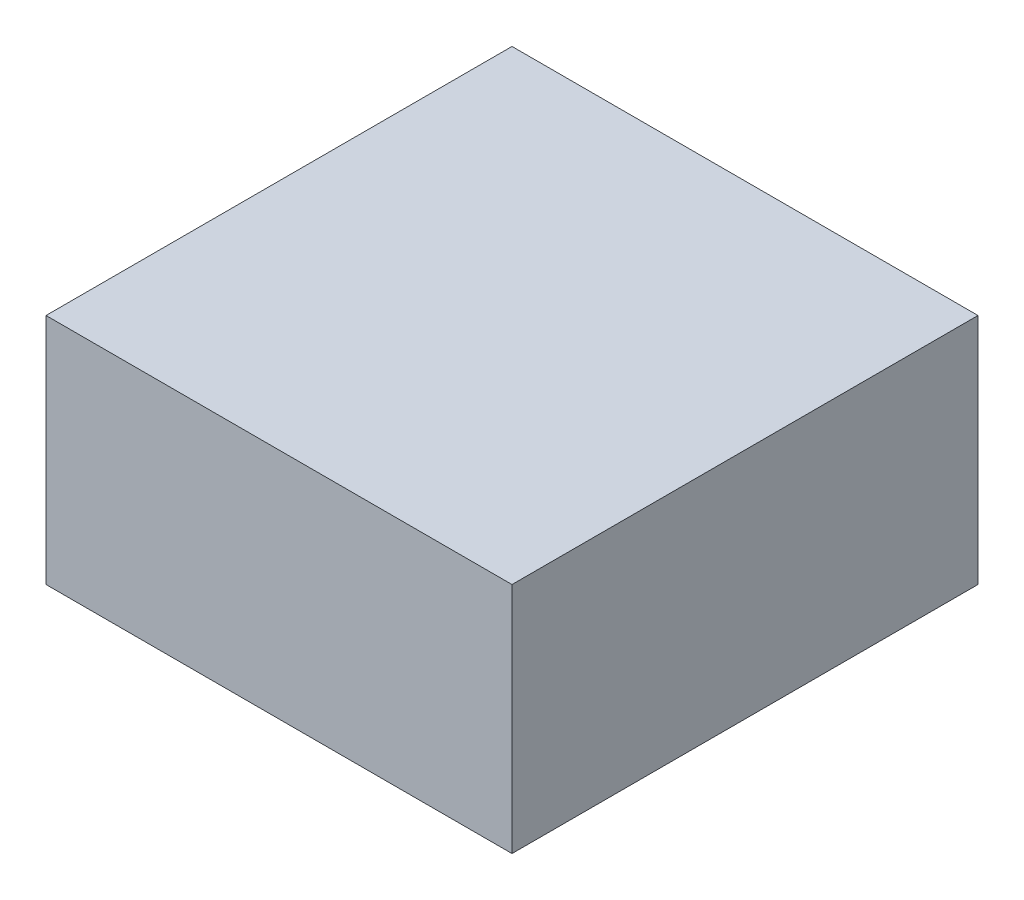
SolidWorks part; units mm, degrees
ref_plane "Plano frontal" through (0, 0, 0) normal (0, 0, 1) x (1, 0, 0)
ref_plane "Plano superior" through (0, 0, 0) normal (0, 1, 0) x (1, 0, 0)
ref_plane "Plano direito" through (0, 0, 0) normal (1, 0, 0) x (0, 0, -1)
sketch "Esboço1" plane through (0, 0, 0) normal (0, 0, 1) x (1, 0, 0)
  line L1 (-4.9673, 1.5327) -> (5.0327, 1.5327)
  line L2 (-4.9673, 1.5327) -> (-4.9673, -3.4673)
  line L3 (-4.9673, -3.4673) -> (5.0327, -3.4673)
  line L4 (5.0327, 1.5327) -> (5.0327, -3.4673)
  dimension "D1" = 10
  dimension "D2" = 5
extrude "Ressalto-extrusão1" add sketch "Esboço1" along normal blind 10
